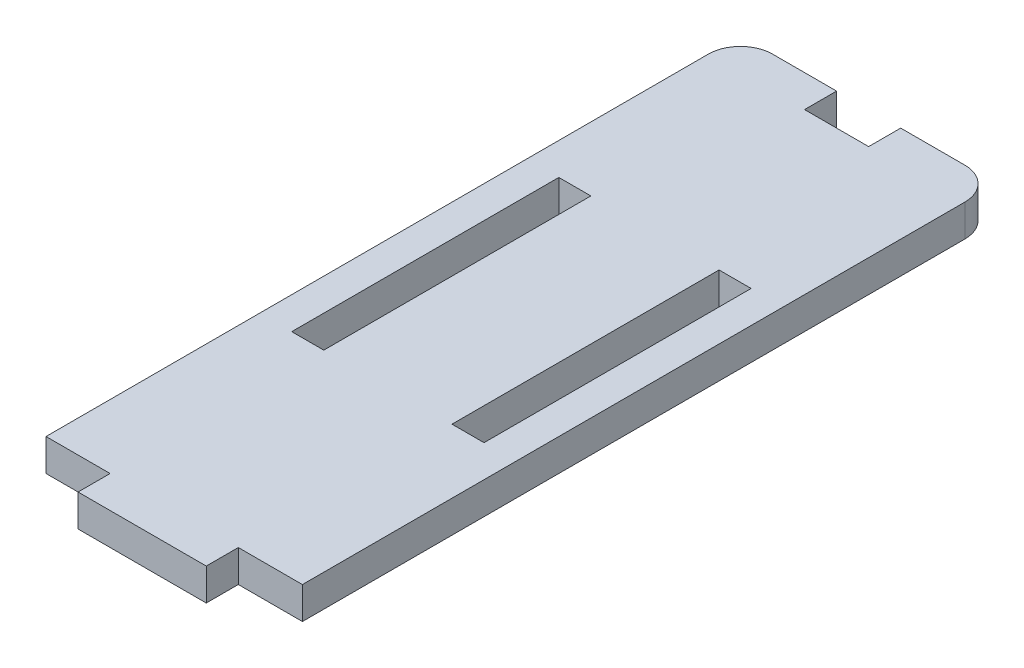
SolidWorks part; units mm, degrees
material "Acrylic (Medium-high impact)"
ref_plane "Plano frontal" through (0, 0, 0) normal (0, 0, 1) x (1, 0, 0)
ref_plane "Plano superior" through (0, 0, 0) normal (0, 1, 0) x (1, 0, 0)
ref_plane "Plano direito" through (0, 0, 0) normal (1, 0, 0) x (0, 0, -1)
sketch "Sketch1" plane through (0, 0, 0) normal (0, 1, 0) x (1, 0, 0)
  line L1 (-12, 32.5) -> (12, 32.5)
  line L2 (-12, 32.5) -> (-12, -32.5)
  line L3 (-12, -32.5) -> (12, -32.5)
  line L4 (12, 32.5) -> (12, -32.5)
  point P4 (-12, 0)
  point P6 (0, 32.5)
  dimension "D1" = 65
  dimension "D2" = 24
extrude "Boss-Extrude1" add sketch "Sketch1" along normal mid plane 3
sketch "Sketch2" plane through (0, 0, 0) normal (0, 1, 0) x (1, 0, 0)
  line L0 (-12, -32.5) -> (12, -32.5) construction
  line L1 (-6, -32.5) -> (6, -32.5)
  line L2 (-6, -32.5) -> (-6, -35.5)
  line L3 (-6, -35.5) -> (6, -35.5)
  line L4 (6, -32.5) -> (6, -35.5)
  line L5 (-12, 32.5) -> (-12, -32.5) construction
  point P6 (0, -35.5)
  dimension "D1" = 3
  dimension "D2" = 12
  dimension "D3" = 6
extrude "Boss-Extrude2" add sketch "Sketch2" along normal mid plane 3
sketch "Sketch4" plane through (0, 0, 0) normal (0, 1, 0) x (1, 0, 0)
  line L0 (-12, 32.5) -> (-12, -32.5) construction
  line L1 (-9, 12.5) -> (-6, 12.5)
  line L2 (-9, 12.5) -> (-9, -12.5)
  line L3 (-9, -12.5) -> (-6, -12.5)
  line L4 (-6, 12.5) -> (-6, -12.5)
  line L5 (0, -1.65) -> (0, 1.65) construction
  line L6 (6, 12.5) -> (6, -12.5)
  line L7 (9, -12.5) -> (6, -12.5)
  line L8 (9, 12.5) -> (9, -12.5)
  line L9 (9, 12.5) -> (6, 12.5)
  point P6 (-6, 0)
  dimension "D1" = 3
  dimension "D2" = 3
  dimension "D3" = 25
extrude "Cut-Extrude1" cut sketch "Sketch4" against normal through all both and the other way through all
fillet "Fillet1" radius 3 2 edges at (12, 0, -32.5) (-12, 0, -32.5)
sketch "Sketch5" plane through (0, 0, 0) normal (0, 1, 0) x (1, 0, 0)
  line L0 (9, 32.5) -> (-9, 32.5) construction
  line L1 (-3, 32.5) -> (3, 32.5)
  line L2 (-3, 32.5) -> (-3, 29.5)
  line L3 (-3, 29.5) -> (3, 29.5)
  line L4 (3, 32.5) -> (3, 29.5)
  point P6 (0, 29.5)
  dimension "D1" = 3
  dimension "D2" = 6
extrude "Cut-Extrude2" cut sketch "Sketch5" against normal through all both and the other way through all
